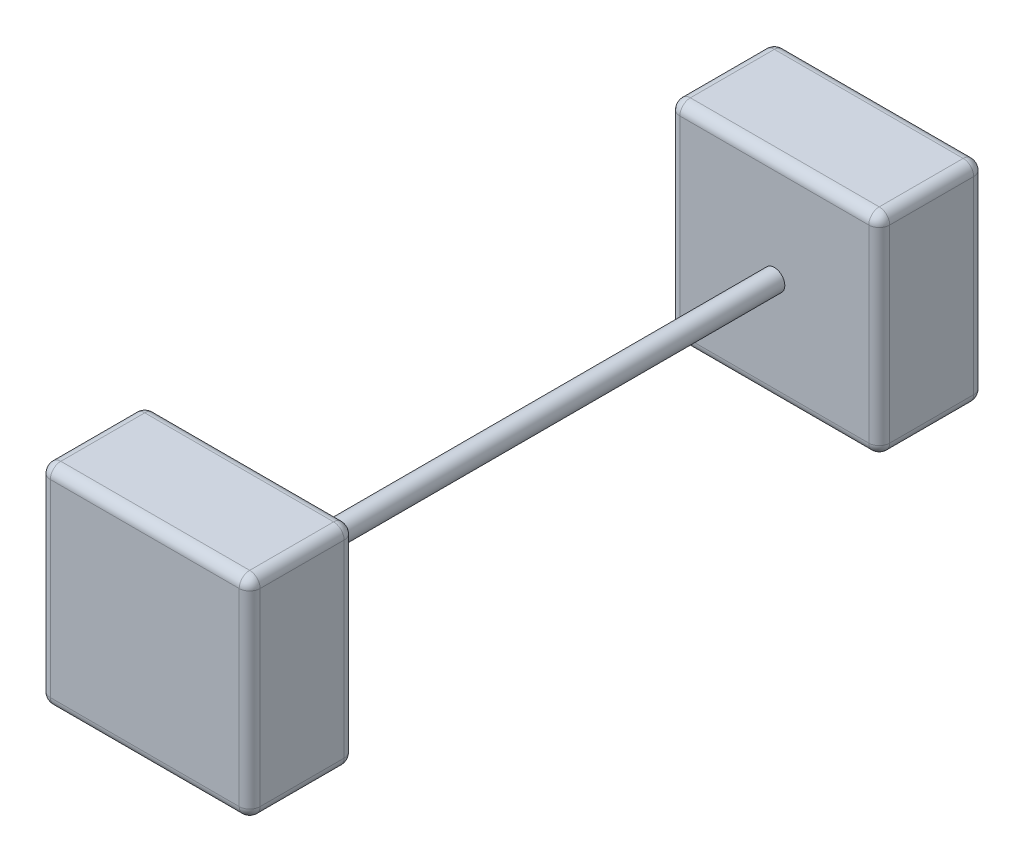
SolidWorks part; units mm, degrees
ref_plane "Front Plane" through (0, 0, 0) normal (0, 0, 1) x (1, 0, 0)
ref_plane "Top Plane" through (0, 0, 0) normal (0, 1, 0) x (1, 0, 0)
ref_plane "Right Plane" through (0, 0, 0) normal (1, 0, 0) x (0, 0, -1)
sketch "Sketch1" plane through (0, 0, 0) normal (0, 0, 1) x (1, 0, 0)
  line L1 (0, 0) -> (20, 0)
  line L2 (0, 0) -> (0, 20)
  line L3 (0, 20) -> (20, 20)
  line L4 (20, 0) -> (20, 20)
  dimension "D1" = 20
  dimension "D2" = 20
extrude "Boss-Extrude1" add sketch "Sketch1" along normal blind 10
sketch "Sketch3" plane through (0, 0, 0) normal (0, -1, 0) x (-1, 0, 0)
  line L0 (0, -10) -> (0, -60)
  line L1 (0, -60) -> (-20, -60)
  line L2 (-20, -60) -> (-20, -10)
  line L3 (-20, -10) -> (0, -10)
  line L9 (0, -60) -> (-20, -60)
  dimension "D1" = 20
  dimension "D2" = 50
sketch "Sketch4" plane through (0, 0, 0) normal (0, 1, 0) x (1, 0, 0)
  line L1 (0, -60) -> (20, -60)
  line L2 (0, -60) -> (0, -70)
  line L3 (0, -70) -> (20, -70)
  line L4 (20, -60) -> (20, -70)
  dimension "D1" = 10
  dimension "D2" = 20
extrude "Boss-Extrude2" add sketch "Sketch4" along normal blind 20 separate body
sketch "Sketch6" plane through (0, 0, 10) normal (0, 0, 1) x (1, 0, 0)
  circle A0 centre (10, 10) radius 1
  dimension "D1" = 2
fillet "Fillet6" radius 1 12 edges at (20, 10, 10) (10, 0, 10) (20, 0, 5) (20, 20, 5) (10, 20, 10) (0, 20, 5) (0, 10, 10) (0, 0, 5) (10, 0, 0) (20, 10, 0) (10, 20, 0) (0, 10, 0)
fillet "Fillet7" radius 1 12 edges at (0, 0, 65) (0, 10, 70) (10, 0, 70) (10, 20, 70) (0, 20, 65) (20, 10, 70) (20, 20, 65) (20, 0, 65) (20, 10, 60) (10, 20, 60) (0, 10, 60) (10, 0, 60)
extrude "Boss-Extrude3" add sketch "Sketch6" along normal up to next (60 mm away)
